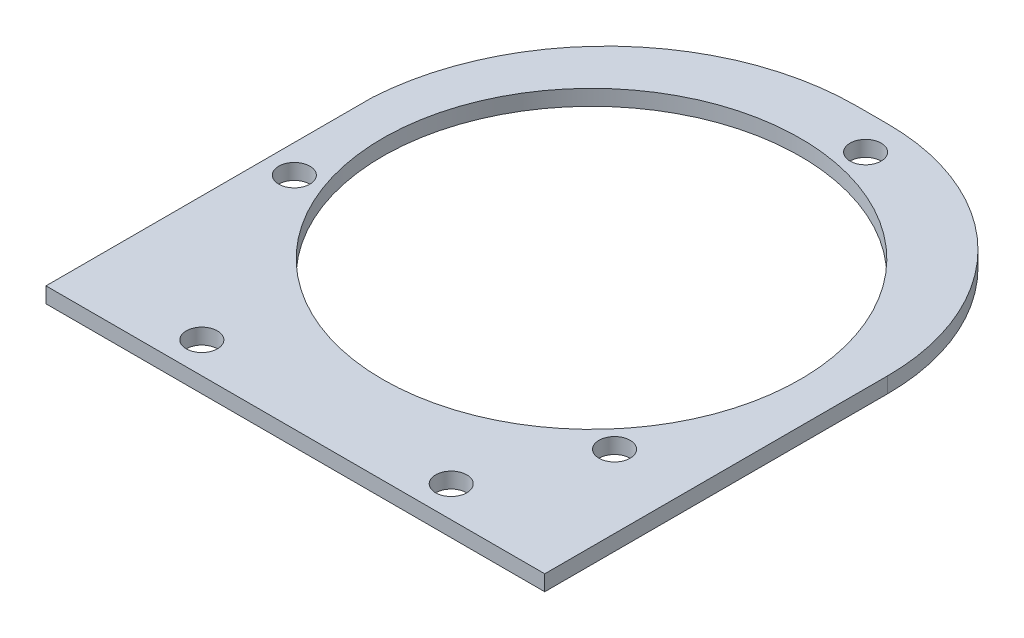
SolidWorks part; units mm, degrees
ref_plane "Front Plane" through (0, 0, 0) normal (0, 0, 1) x (1, 0, 0)
ref_plane "Top Plane" through (0, 0, 0) normal (0, 1, 0) x (1, 0, 0)
ref_plane "Right Plane" through (0, 0, 0) normal (1, 0, 0) x (0, 0, -1)
sketch "Sketch1" plane through (0, 0, 0) normal (0, 1, 0) x (1, 0, 0)
  line L0 (0, 114.3) -> (0, -114.3) construction
  line L1 (12.7, 114.3) -> (0, 114.3)
  line L2 (101.6, 25.4) -> (101.6, -114.3)
  line L3 (101.6, -114.3) -> (-101.6, -114.3)
  line L4 (-101.6, 18.6765) -> (-101.6, -114.3)
  line L5 (101.6, 114.3) -> (-101.6, -114.3) construction
  line L6 (101.6, -114.3) -> (-101.6, 114.3) construction
  line L7 (-101.6, 6.35) -> (101.6, 6.35) construction
  line L8 (0, 6.35) -> (-101.6, -28.6337) construction
  line L9 (-101.6, -101.6) -> (101.6, -101.6) construction
  circle A0 centre (0, 6.35) radius 85.09
  circle A1 centre (0, 6.35) radius 95.25 construction
  circle A2 centre (-90.0606, -24.6604) radius 6.35
  circle A3 centre (-50.8, -101.6) radius 6.35
  circle A4 centre (50.8, -101.6) radius 6.35
  circle A5 centre (18.1746, 99.85) radius 6.35
  circle A6 centre (71.8861, -56.1396) radius 6.35
  arc A7 (0, 114.3) -> (-101.6, 18.6765) centre (0, 12.5132) ccw
  arc A8 (12.7, 114.3) -> (101.6, 25.4) centre (12.7, 25.4) cw
  point P0 (0, 0)
  point P11 (0, 6.35)
  point P30 (0, 6.35)
  point P32 (0, 6.35)
  dimension "D3" = 170.18
  dimension "D5" = 190.5
  dimension "D6" = 12.7
  dimension "D7" = 12.7
  dimension "D8" = 12.7
  dimension "D11" = 88.9
  dimension "D1" = 228.6
  dimension "D2" = 120.65
  dimension "D4" = 19
  dimension "D9" = 50.8
  dimension "D10" = 203.2
extrude "Boss-Extrude1" add sketch "Sketch1" along normal blind 6.35
sketch "Sketch2" plane through (0, 6.35, 0) normal (0, 1, 0) x (1, 0, 0)
  line L0 (-101.6, 18.6765) -> (-101.6, -114.3) construction
  line L2 (101.6, -167.64) -> (-101.6, -167.64)
  line L5 (101.6, -167.64) -> (101.6, 114.3)
  line L6 (101.6, 114.3) -> (-101.6, 114.3)
  line L7 (-101.6, -114.3) -> (101.6, -114.3) construction
  line L8 (101.6, -114.3) -> (101.6, 25.4) construction
  line L9 (12.7, 114.3) -> (0, 114.3) construction
  line L10 (-101.6, 18.6765) -> (-101.6, -114.3)
  line L11 (-101.6, -114.3) -> (101.6, -114.3)
  line L12 (101.6, -114.3) -> (101.6, 25.4)
  line L13 (12.7, 114.3) -> (0, 114.3)
  line L14 (-101.6, -167.64) -> (-101.6, 114.3)
  line L15 (101.6, -167.64) -> (-139.7, -167.64)
  line L16 (101.6, -167.64) -> (101.6, 115.3414)
  line L17 (101.6, 115.3414) -> (-139.7, 115.3414)
  line L18 (-139.7, -167.64) -> (-139.7, 115.3414)
  point P0 (0, 0)
  dimension "D1" = 1.0414
  dimension "D2" = 53.34
  dimension "D3" = 228.6
  dimension "D4" = 203.2
  dimension "D5" = 241.3
  dimension "D6" = 282.9814
